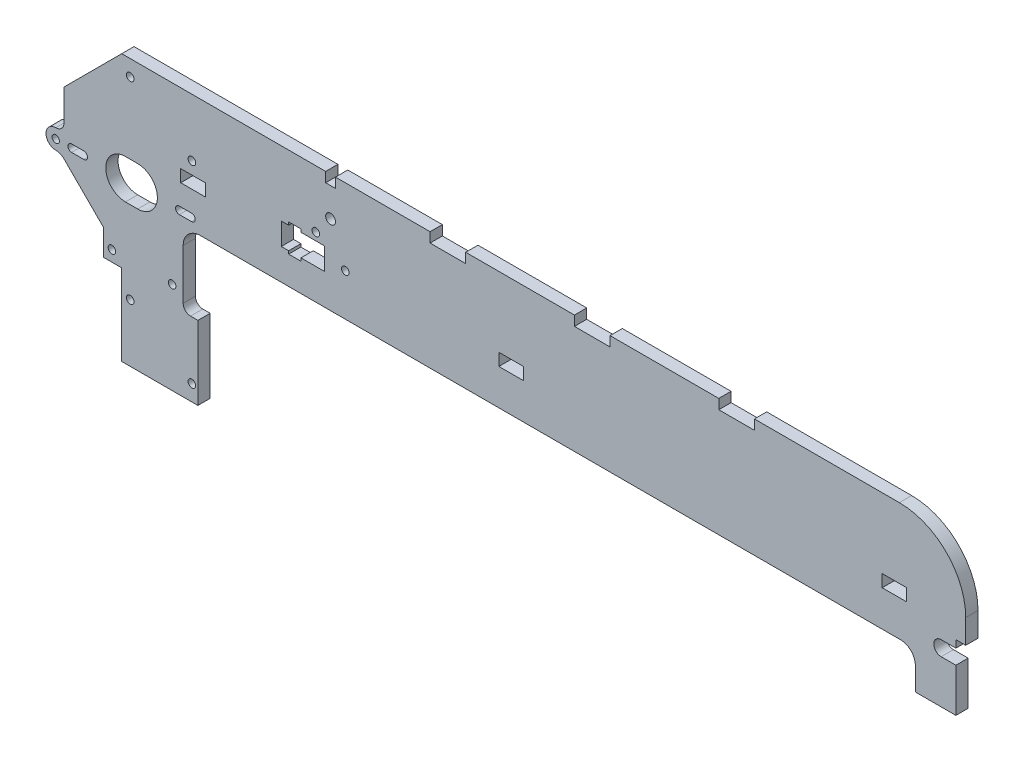
SolidWorks part; units mm, degrees
material "6061-T6 Black anodised"
ref_plane "Front Plane" through (0, 0, 0) normal (0, 0, 1) x (1, 0, 0)
ref_plane "Top Plane" through (0, 0, 0) normal (0, 1, 0) x (1, 0, 0)
ref_plane "Right Plane" through (0, 0, 0) normal (1, 0, 0) x (0, 0, -1)
sketch "Sketch1" plane through (0, 0, 0) normal (0, 0, 1) x (1, 0, 0)
  line L0 (-19.5, 0) -> (36.1968, 0) construction
  line L1 (-1.5, 32) -> (20.5, 32) construction
  line L2 (-21.9203, 0) -> (-30, 0) construction
  line L3 (-6.5, 43.5) -> (-6.5, 28.8553) construction
  line L4 (-1.5, 43.5) -> (20.5, 43.5) construction
  line L5 (310, 43.5) -> (251, 43.5)
  line L6 (21.9203, 0) -> (0, 21.9203) construction
  line L7 (0, 21.9203) -> (-21.9203, 0) construction
  line L8 (-21.9203, 0) -> (0, -21.9203) construction
  line L9 (0, -21.9203) -> (21.9203, 0) construction
  line L10 (316.5, -4.6) -> (316.5, -20)
  line L11 (-6.5, -65) -> (-6.5, -32)
  line L12 (-30, 5.3553) -> (-30, -5.3553) construction
  line L13 (327, 3.7) -> (333, 3.7)
  line L14 (316.5, -20) -> (333, -20)
  line L15 (18.5, -4.6) -> (316.5, -4.6)
  line L16 (34.5, -11.1) -> (59.432, -11.1) construction
  line L17 (333, 6.7) -> (333, 3.7)
  line L18 (9.5, 43.5) -> (9.5, -35.4767) construction
  line L19 (-1.5, 43.5) -> (20.5, 43.5) construction
  line L20 (-1.5, 43.5) -> (-1.5, 20.5) construction
  line L21 (-6.5, -65) -> (24.5, -65)
  line L22 (-1.5, 20.5) -> (20.5, 20.5) construction
  line L23 (327, -2.3) -> (333, -2.3)
  line L24 (333, -2.3) -> (333, -20)
  line L25 (333, 6.7) -> (337, 6.7)
  line L26 (337, 6.7) -> (337, 16.5)
  line L27 (18.5, -35) -> (18.5, -4.6)
  line L28 (20.5, 43.5) -> (20.5, 20.5) construction
  line L29 (17.5, 15) -> (17.5, 10)
  line L30 (17.5, 15) -> (27.5, 15)
  line L31 (27, 72.5933) -> (67, 72.5933) construction
  line L32 (147, 10) -> (157, 10)
  line L33 (147, 10) -> (147, 15)
  line L34 (17.5, 10) -> (27.5, 10)
  line L35 (27.5, 15) -> (27.5, 10)
  line L36 (147, 15) -> (157, 15)
  line L37 (157, 10) -> (157, 15)
  line L38 (303, 10) -> (313, 10)
  line L39 (303, 10) -> (303, 15)
  line L40 (303, 15) -> (313, 15)
  line L41 (313, 10) -> (313, 15)
  line L42 (27, 72.5933) -> (27, -81.6129) construction
  line L43 (27, -81.6129) -> (67, -81.6129) construction
  line L44 (67, 72.5933) -> (67, -81.6129) construction
  line L45 (-1.5, -52.5) -> (20.5, -52.5) construction
  line L46 (-1.5, -65) -> (20.5, -65) construction
  line L47 (-1.5, -65) -> (-1.5, -42) construction
  line L48 (-1.5, -42) -> (20.5, -42) construction
  line L49 (20.5, -65) -> (20.5, -42) construction
  line L50 (58.4277, 8) -> (61.4277, 8)
  line L51 (27.5, 12.5) -> (63.9277, 12.5) construction
  line L52 (61.4277, 6.8061) -> (66.4277, 6.8061)
  line L53 (61.4277, 6.8061) -> (61.4277, 8)
  line L54 (76, 8) -> (76, 17)
  line L55 (72.5, 20.1) -> (72.5, 7.1) construction
  line L56 (66.4277, 6.8061) -> (66.4277, 8)
  line L57 (66.4277, 8) -> (76, 8)
  line L58 (63.9277, 12.5) -> (76, 12.5) construction
  line L59 (66.4277, 18.1939) -> (61.4277, 18.1939)
  line L60 (66.4277, 6.8061) -> (61.4277, 18.1939) construction
  line L61 (61.4277, 6.8061) -> (66.4277, 18.1939) construction
  line L62 (18.5, -35) -> (24.5, -35)
  line L63 (66.4277, 17) -> (66.4277, 18.1939)
  line L64 (66.4277, 17) -> (76, 17)
  line L65 (61.4277, 17) -> (61.4277, 18.1939)
  line L66 (24.5, -35) -> (24.5, -65)
  line L67 (-14, -21.3553) -> (-30, -5.3553)
  line L68 (-14, -21.3553) -> (-14, -32)
  line L69 (-14, -32) -> (-6.5, -32)
  line L70 (119, 43.5) -> (119, 39.5)
  line L71 (119, 39.5) -> (133.5, 39.5)
  line L72 (177.75, 43.5) -> (177.75, 39.5)
  line L73 (119, 43.5) -> (80.5, 43.5)
  line L74 (-6.5, 28.8553) -> (-30, 5.3553) construction
  line L75 (177.75, 39.5) -> (192.25, 39.5)
  line L76 (159.788, -14) -> (-14, -14) construction
  line L77 (159.788, -14) -> (159.788, -26) construction
  line L78 (61.4277, 17) -> (58.4277, 17)
  line L79 (159.788, -26) -> (-14, -26) construction
  line L80 (-14, -14) -> (-14, -26) construction
  line L81 (58.4277, 17) -> (58.4277, 8)
  line L82 (159.788, -14) -> (-14, -26) construction
  line L83 (159.788, -26) -> (-14, -14) construction
  line L84 (192.25, 39.5) -> (192.25, 43.5)
  line L86 (236.5, 43.5) -> (236.5, 39.5)
  line L87 (236.5, 39.5) -> (251, 39.5)
  line L88 (251, 39.5) -> (251, 43.5)
  line L89 (177.75, 43.5) -> (133.5, 43.5)
  line L91 (-33.3631, 8.7185) -> (-33.3631, -8.7185) construction
  line L92 (76.5, 27.7514) -> (80.5, 27.7514) construction
  line L93 (133.5, 39.5) -> (133.5, 43.5)
  line L94 (76.5, 43.5) -> (76.5, 39.5)
  line L95 (76.5, 39.5) -> (80.5, 39.5)
  line L96 (80.5, 43.5) -> (80.5, 39.5)
  line L97 (76.5, 43.5) -> (-6.5, 43.5)
  line L98 (-30, 20) -> (-6.5, 43.5)
  line L99 (-30, 20) -> (-30, 7.3254)
  line L101 (119, 43.5) -> (177.75, 43.5) construction
  line L102 (192.25, 43.5) -> (236.5, 43.5)
  circle A0 centre (9.5, 34.5) radius 1.55 construction
  circle A1 centre (0, 0) radius 15.5 construction
  circle A2 centre (0, 21.9203) radius 1.5 construction
  circle A3 centre (21.9203, 0) radius 1.5
  circle A4 centre (0, -21.9203) radius 1.5 construction
  circle A5 centre (-21.9203, 0) radius 1.5
  circle A6 centre (0, 0) radius 5.5 construction
  arc A7 (337, 16.5) -> (310, 43.5) centre (310, 16.5) ccw
  circle A8 centre (0, 0) radius 8
  circle A9 centre (-3.05, 37) radius 1.55
  circle A10 centre (9.5, -57) radius 1.55 construction
  arc A11 (327, 3.7) -> (327, -2.3) centre (327, 0.7) ccw
  circle A12 centre (72, 0.4) radius 5 construction
  circle A13 centre (22, 38.5) radius 5 construction
  circle A14 centre (22, 38.5) radius 1.5 construction
  circle A15 centre (72, 0.4) radius 1.5 construction
  circle A16 centre (22.05, 20) radius 1.55
  circle A17 centre (-3.05, -41.5) radius 1.55
  circle A18 centre (22.05, -58.5) radius 1.55
  circle A19 centre (81.5, 20.1) radius 1.55 construction
  circle A20 centre (72.5, 20.1) radius 1.55
  circle A21 centre (84.5, 12.5) radius 1.55
  circle A22 centre (-10.5, -27.55) radius 1.55
  arc A23 (-33.3631, 3.9623) -> (-33.3631, -3.9623) centre (-33.3631, 0) ccw
  circle A24 centre (14, -27.55) radius 1.55
  circle A25 centre (-33.3631, 0) radius 1.5
  arc A26 (-33.3631, 3.9623) -> (-30, 7.3254) centre (-33.3631, 7.3254) ccw
  arc A27 (-33.3631, -3.9623) -> (-30, -5.3553) centre (-33.3631, -8.7185) cw
  circle A28 centre (78.5, 27.7514) radius 2
  point P18 (26.8692, -2.8293)
  point P19 (26.8692, 2.8293)
  point P108 (58.4277, 12.5)
  point P115 (72.894, -20)
  dimension "D2" = 31
  dimension "D3" = 3
  dimension "D4" = 11
  dimension "D12" = 16
  dimension "D20" = 3.1
  dimension "D25" = 3
  dimension "D32" = 10
  dimension "D38" = 3
  dimension "D41" = 3.1
  dimension "D45" = 3.1
  dimension "D57" = 3.1
  dimension "D69" = 4
  dimension "D6" = 4.6
  dimension "D10" = 6.5
  dimension "D11" = 16.5
  dimension "D8" = 65
  dimension "D9" = 43.5
  dimension "D19" = 30
  dimension "D21" = 9
  dimension "D22" = 8
  dimension "D23" = 21.1
  dimension "D24" = 15.4
  dimension "D26" = 6
  dimension "D27" = 4
  dimension "D28" = 6
  dimension "D30" = 17.5
  dimension "D33" = 5
  dimension "D34" = 10
  dimension "D35" = 24
  dimension "D36" = 180
  dimension "D29" = 67
  dimension "D31" = 40
  dimension "D7" = 9
  dimension "D5" = 9.5
  dimension "D13" = 337
  dimension "D15" = 23
  dimension "D37" = 22
  dimension "D39" = 5
  dimension "D40" = 12
  dimension "D42" = 11
  dimension "D43" = 6
  dimension "D50" = 5
  dimension "D59" = 3
  dimension "D60" = 9
  dimension "D46" = 3.1
  dimension "D47" = 9
  dimension "D44" = 9
  dimension "D49" = 0.7
  dimension "D51" = 12
  dimension "D52" = 3.5
  dimension "D16" = 25
  dimension "D14" = 31
  dimension "D17" = 15
  dimension "D55" = 12
  dimension "D56" = 20
  dimension "D58" = 4.5
  dimension "D18" = 7.5
  dimension "D53" = 6
  dimension "D54" = 4
  dimension "D48" = 15
  dimension "D61" = 30
  dimension "D62" = 12.5
  dimension "D68" = 4
  dimension "D70" = 6
  dimension "D64" = 14.5
  dimension "D72" = 58.75
  dimension "D63" = 52
  dimension "D67" = 3
extrude "Boss-Extrude1" add sketch "Sketch1" along normal blind 5
fillet "Fillet1" [suppressed] radius 8
fillet "Fillet2" radius 7 1 edges at (18.5, -4.6, 2.5)
fillet "Fillet3" radius 3 1 edges at (18.5, -35, 2.5)
sketch "Sketch2" plane through (0, 0, 5) normal (0, 0, 1) x (1, 0, 0)
  line L0 (21.9203, 0) -> (16.9203, 0) construction
  line L1 (21.9203, -1.5) -> (16.9203, -1.5)
  line L2 (21.9203, 1.5) -> (16.9203, 1.5)
  line L3 (0, 0) -> (-5, 0) construction
  line L4 (0, -8) -> (-5, -8)
  line L5 (0, 8) -> (-5, 8)
  line L6 (-21.9203, 0) -> (-26.9203, 0) construction
  line L7 (-21.9203, -1.5) -> (-26.9203, -1.5)
  line L8 (-21.9203, 1.5) -> (-26.9203, 1.5)
  arc A0 (21.9203, -1.5) -> (21.9203, 1.5) centre (21.9203, 0) ccw
  arc A1 (16.9203, 1.5) -> (16.9203, -1.5) centre (16.9203, 0) ccw
  arc A2 (0, -8) -> (0, 8) centre (0, 0) ccw
  arc A3 (-5, 8) -> (-5, -8) centre (-5, 0) ccw
  arc A4 (-21.9203, -1.5) -> (-21.9203, 1.5) centre (-21.9203, 0) ccw
  arc A5 (-26.9203, 1.5) -> (-26.9203, -1.5) centre (-26.9203, 0) ccw
  circle A6 centre (21.9203, 0) radius 1.5 construction
  circle A7 centre (0, 0) radius 8 construction
  point P4 (19.4203, 0)
  point P9 (-2.5, 0)
  point P16 (-24.4203, 0)
  dimension "D1" = 5
extrude "Cut-Extrude1" cut sketch "Sketch2" against normal through all
fillet "Fillet4" radius 6 1 edges at (316.5, -4.6, 2.5)
sketch "Sketch3" plane through (0, 0, 5) normal (0, 0, 1) x (1, 0, 0)
  line L0 (-12.375, 32.625) -> (-12.375, 37.625) construction
  line L1 (-13.125, 42.8359) -> (-11.625, 42.8359)
  line L2 (-13.125, 42.8359) -> (-13.125, 33.924)
  line L3 (-6.5, 43.5) -> (-30, 20) construction
  line L4 (-11.625, 42.8359) -> (-11.625, 33.924)
  line L5 (-13.125, 42.8359) -> (-11.625, 33.924) construction
  line L6 (-13.125, 33.924) -> (-11.625, 42.8359) construction
  line L7 (-6.5, 43.5) -> (-12.375, 37.625) construction
  line L8 (-12.375, 37.625) -> (-18.25, 31.75) construction
  line L9 (-18.25, 31.75) -> (-24.125, 25.875) construction
  line L10 (-24.125, 25.875) -> (-30, 20) construction
  line L11 (-17.4, 36.9218) -> (-17.4, 27.9859)
  line L12 (-18.25, 26.75) -> (-18.25, 31.75) construction
  line L13 (-19.1, 36.9218) -> (-17.4, 27.9859) construction
  line L14 (-19.1, 27.9859) -> (-17.4, 36.9218) construction
  line L15 (-19.1, 36.9218) -> (-19.1, 27.9859)
  line L16 (-19.1, 36.9218) -> (-17.4, 36.9218)
  line L17 (-23.275, 31.0468) -> (-23.275, 22.1109)
  line L18 (-24.975, 31.0468) -> (-23.275, 22.1109) construction
  line L19 (-24.975, 22.1109) -> (-23.275, 31.0468) construction
  line L20 (-24.975, 31.0468) -> (-23.275, 31.0468)
  line L21 (-24.125, 20.875) -> (-24.125, 25.875) construction
  line L22 (-24.975, 31.0468) -> (-24.975, 22.1109)
  arc A0 (-13.125, 33.924) -> (-11.625, 33.924) centre (-12.375, 32.625) ccw
  arc A1 (-19.1, 27.9859) -> (-17.4, 27.9859) centre (-18.25, 26.75) ccw
  arc A2 (-24.975, 22.1109) -> (-23.275, 22.1109) centre (-24.125, 20.875) ccw
  point P0 (-12.375, 38.3799)
  point P15 (-18.25, 32.4539)
  point P22 (-24.125, 26.5789)
  dimension "D1" = 1.5
  dimension "D2" = 1.5
  dimension "D3" = 5
extrude "Cut-Extrude2" [suppressed] cut sketch "Sketch3" against normal through all
fillet "Fillet5" [suppressed] radius 0.5
equation "\"y-plate-thickness\"=5"
equation "\"bed-plate-thickness\"=6"
equation "\"x-plate-thickness\"=5"
equation "\"D1@Boss-Extrude1\"=\"x-plate-thickness\""
equation "\"D33@Sketch1\"=\"x-plate-thickness\""
